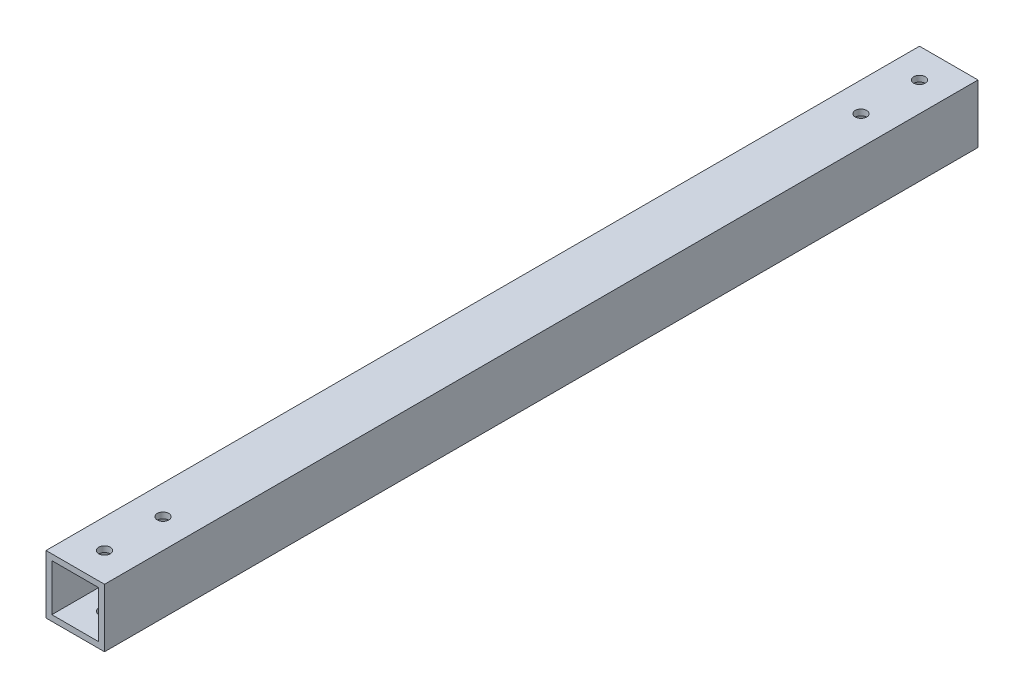
SolidWorks part; units mm, degrees
ref_plane "Front Plane" through (0, 0, 0) normal (0, 0, 1) x (1, 0, 0)
ref_plane "Top Plane" through (0, 0, 0) normal (0, 1, 0) x (1, 0, 0)
ref_plane "Right Plane" through (0, 0, 0) normal (1, 0, 0) x (0, 0, -1)
sketch "Sketch1" plane through (0, 0, 0) normal (0, 0, 1) x (1, 0, 0)
  line L1 (0, 0) -> (25.4, 0)
  line L2 (0, 0) -> (0, 25.4)
  line L3 (0, 25.4) -> (25.4, 25.4)
  line L4 (25.4, 0) -> (25.4, 25.4)
  dimension "D1" = 25.4
  dimension "D2" = 25.4
extrude "Extrude-Thin1" add sketch "Sketch1" along normal mid plane 379.1636 thin thin type one direction reverse wall 2.54
sketch "Sketch2" plane through (0, 25.4, 0) normal (0, 1, 0) x (1, 0, 0)
  line L0 (12.7, -189.5818) -> (12.7, 189.5818) construction
  line L1 (25.4, -189.5818) -> (0, -189.5818) construction
  line L2 (25.4, 189.5818) -> (0, 189.5818) construction
  line L3 (0, 0) -> (25.4, 0) construction
  line L4 (0, -189.5818) -> (0, 189.5818) construction
  line L5 (25.4, -189.5818) -> (25.4, 189.5818) construction
  circle A0 centre (12.7, -176.8818) radius 2.4892
  circle A1 centre (12.7, -151.4818) radius 2.4892
  circle A2 centre (12.7, 176.8818) radius 2.4892
  circle A3 centre (12.7, 151.4818) radius 2.4892
  dimension "D1" = 4.9784
  dimension "D2" = 12.7
  dimension "D3" = 25.4
extrude "Cut-Extrude1" cut sketch "Sketch2" against normal through all
